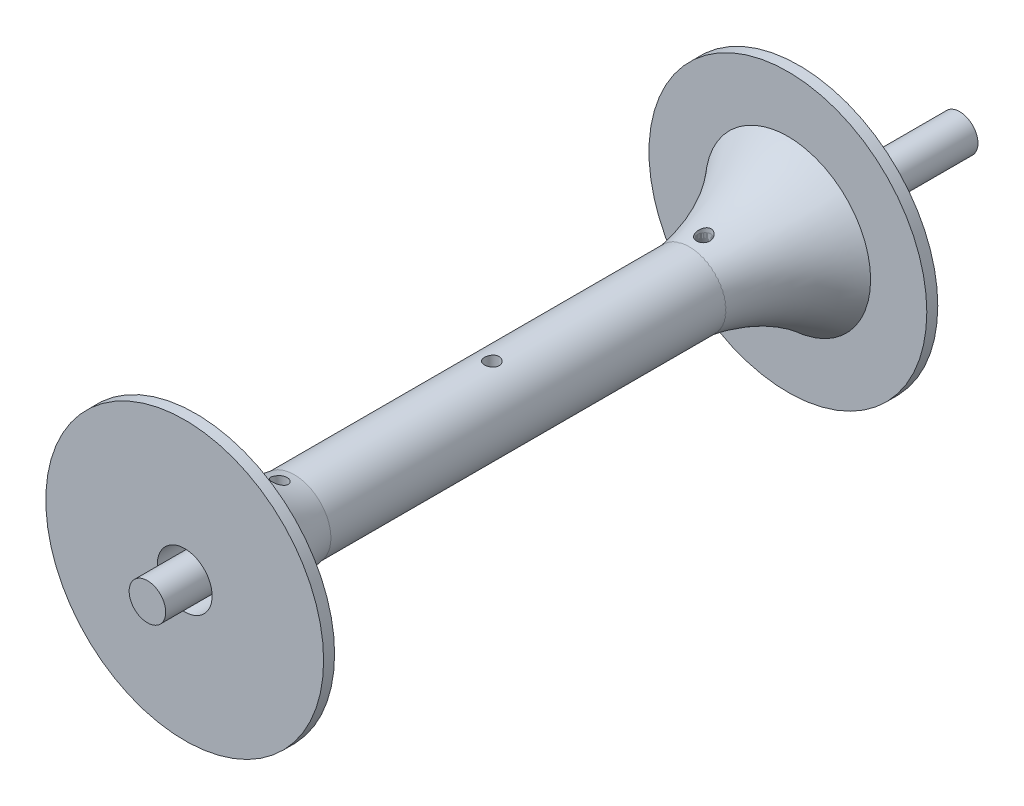
SolidWorks part; units mm, degrees
ref_plane "Front Plane" through (0, 0, 0) normal (0, 0, 1) x (1, 0, 0)
ref_plane "Top Plane" through (0, 0, 0) normal (0, 1, 0) x (1, 0, 0)
ref_plane "Right Plane" through (0, 0, 0) normal (1, 0, 0) x (0, 0, -1)
sketch "Sketch1" plane through (0, 0, 0) normal (0, 0, 1) x (1, 0, 0)
  circle A0 centre (0, 0) radius 6.35
  dimension "D1" = 12.7
extrude "Boss-Extrude1" add sketch "Sketch1" along normal blind 282.194
ref_plane "Plane1" through (0, 0, 5.08) normal (0, 0, -1) x (-1, 0, 0)
sketch "Sketch3" plane through (0, 0, 5.08) normal (0, 0, -1) x (-1, 0, 0)
  circle A0 centre (0, 0) radius 30.48
  dimension "D1" = 60.96
ref_plane "Plane2" through (0, 0, 55.88) normal (0, 0, -1) x (-1, 0, 0)
sketch "Sketch4" plane through (0, 0, 55.88) normal (0, 0, -1) x (-1, 0, 0)
  circle A0 centre (0, 0) radius 9.525
  dimension "D1" = 19.05
ref_plane "Plane3" through (0, 0, 141.097) normal (0, 0, 1) x (1, 0, 0)
ref_axis "Axis1" through (0, 0, 282.194) along (0, 0, -1)
sketch "Sketch8" plane through (0, 0, 55.88) normal (0, 0, -1) x (-1, 0, 0)
  circle A0 centre (0, 0) radius 12.7
  dimension "D1" = 25.4
sketch "Sketch11" plane through (0, 0, 55.88) normal (0, 0, -1) x (-1, 0, 0)
  circle A0 centre (0, 0) radius 30.48
  dimension "D1" = 60.96
ref_plane "Plane4" through (0, 0, 106.68) normal (0, 0, -1) x (-1, 0, 0)
sketch "Sketch12" plane through (0, 0, 106.68) normal (0, 0, -1) x (-1, 0, 0)
  circle A0 centre (0, 0) radius 9.525
  dimension "D1" = 19.05
sketch "Sketch14" plane through (0, 0, 0) normal (1, 0, 0) x (0, 0, -1)
  line L0 (-106.68, -6.7056) -> (-106.68, 6.7056) construction
  line L1 (-55.88, -30.48) -> (-55.88, 30.48) construction
  line L2 (-106.68, 9.525) -> (-55.88, 9.525)
  line L3 (-106.68, -9.525) -> (-106.68, 9.525) construction
  line L4 (-55.88, -9.525) -> (-55.88, 9.525) construction
  line L5 (-55.88, 9.525) -> (-55.88, 32.385)
  line L6 (-106.68, 12.065) -> (-106.68, 9.525)
  line L7 (-106.68, 9.525) -> (-55.88, 9.525) construction
  line L8 (-282.194, 0) -> (0, 0) construction
  arc A0 (-106.68, 12.065) -> (-55.88, 32.385) centre (-103.6033, 78.0333) ccw
  dimension "D1" = 66.04
  dimension "D2" = 22.86
  dimension "D3" = 9.525
  dimension "D4" = 2.54
revolve "Revolve1" add sketch "Sketch14" angle 360 about axis through (0, 0, 282.194) along (0, 0, -1)
ref_plane "Plane5" through (0, 0, 162.56) normal (0, 0, -1) x (-1, 0, 0)
sketch "Sketch15" plane through (0, 0, 0) normal (1, 0, 0) x (0, 0, -1)
  line L0 (-55.88, -30.48) -> (-55.88, 30.48) construction
  line L1 (-55.88, 22.86) -> (-59.69, 22.86)
  line L2 (-55.88, 22.86) -> (-55.88, 48.26)
  line L3 (-55.88, 48.26) -> (-59.69, 48.26)
  line L4 (-59.69, 22.86) -> (-59.69, 48.26)
  line L5 (-282.194, 0) -> (0, 0) construction
  dimension "D1" = 25.4
  dimension "D2" = 3.81
  dimension "D3" = 22.86
revolve "Revolve2" add sketch "Sketch15" angle 360 about axis through (0, 0, 282.194) along (0, 0, -1)
extrude "Boss-Extrude2" add sketch "Sketch8" against normal blind 184.658 separate body contours A0
mirror "Mirror6" about plane through (0, 0, 162.56) normal (0, 0, -1) of "Revolve2", "Revolve1"
sketch "Sketch16" plane through (0, 0, 0) normal (0, 1, 0) x (1, 0, 0)
  line L0 (0, -282.194) -> (0, 0) construction
  line L1 (35.6235, -162.56) -> (-35.6235, -162.56) construction
  circle A0 centre (0, -88.9) radius 2.54
  circle A1 centre (0, -162.56) radius 2.54
  circle A2 centre (0, -236.22) radius 2.54
  dimension "D1" = 5.08
  dimension "D2" = 5.08
  dimension "D3" = 5.08
  dimension "D4" = 73.66
  dimension "D5" = 73.66
extrude "Cut-Extrude1" cut sketch "Sketch16" against normal through all both and the other way through all
equation "\"A\"=0.5"
equation "\"D1@Sketch1\"=\"A\""
equation "\"B\"=0.2"
equation "\"D1@Sketch16\"=\"B\""
